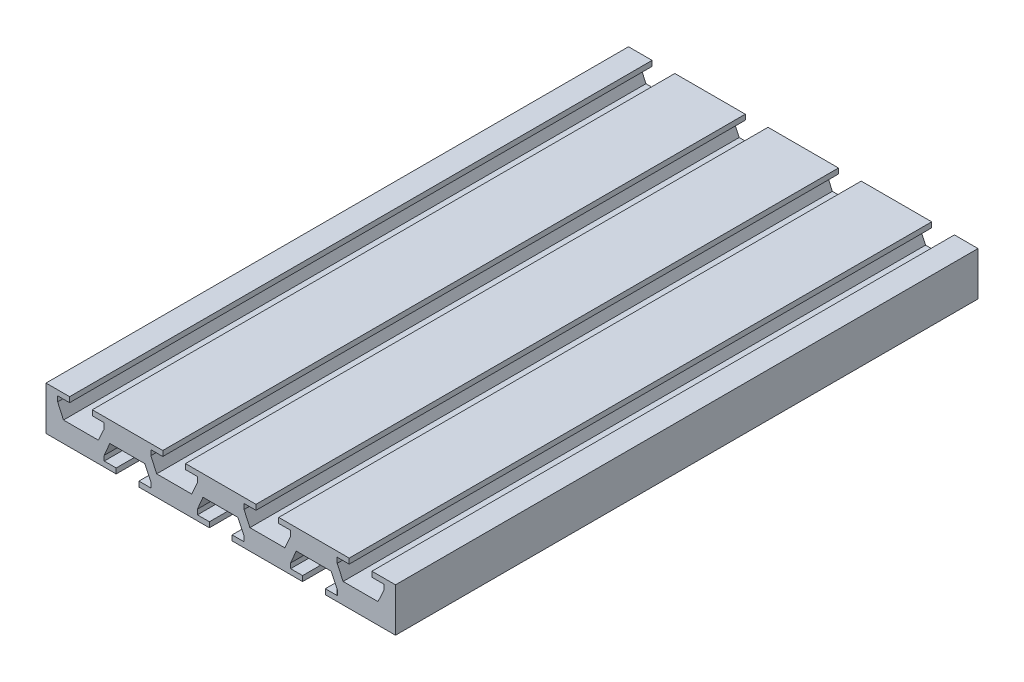
SolidWorks part; units mm, degrees
ref_plane "Front Plane" through (0, 0, 0) normal (0, 0, 1) x (1, 0, 0)
ref_plane "Top Plane" through (0, 0, 0) normal (0, 1, 0) x (1, 0, 0)
ref_plane "Right Plane" through (0, 0, 0) normal (1, 0, 0) x (0, 0, -1)
sketch "Sketch1" plane through (0, 0, 0) normal (0, 0, 1) x (1, 0, 0)
  line L0 (-48, 7.5) -> (-48, -0.5) construction
  line L1 (60, -7.5) -> (35.9, -7.5)
  line L2 (60, -7.5) -> (60, 7.5)
  line L3 (60, 7.5) -> (51.9, 7.5)
  line L4 (-60, -7.5) -> (-60, 7.5)
  line L5 (-24, -3.9) -> (-26.0998, 0.5)
  line L8 (-44.1, 7.5) -> (-44.1, 5.7)
  line L9 (-44.1, 5.7) -> (-40, 5.7)
  line L10 (-40, 5.7) -> (-40, 3.9)
  line L11 (-40, 3.9) -> (-42, -0.5)
  line L12 (-42, -0.5) -> (-54, -0.5)
  line L13 (-56, 3.9) -> (-54, -0.5)
  line L14 (-56, 5.7) -> (-56, 3.9)
  line L15 (-51.9, 5.7) -> (-56, 5.7)
  line L16 (-51.9, 7.5) -> (-51.9, 5.7)
  line L17 (-10, -0.5) -> (-22, -0.5)
  line L18 (-24, 3.9) -> (-22, -0.5)
  line L19 (-24, 5.7) -> (-24, 3.9)
  line L20 (-19.9, 5.7) -> (-24, 5.7)
  line L21 (-19.9, 7.5) -> (-19.9, 5.7)
  line L23 (-12.1, 7.5) -> (-12.1, 5.7)
  line L24 (-12.1, 5.7) -> (-8, 5.7)
  line L25 (-8, 5.7) -> (-8, 3.9)
  line L26 (-8, 3.9) -> (-10, -0.5)
  line L27 (22, -0.5) -> (10, -0.5)
  line L28 (8, 3.9) -> (10, -0.5)
  line L29 (8, 5.7) -> (8, 3.9)
  line L30 (12.1, 5.7) -> (8, 5.7)
  line L31 (12.1, 7.5) -> (12.1, 5.7)
  line L33 (19.9, 7.5) -> (19.9, 5.7)
  line L34 (19.9, 5.7) -> (24, 5.7)
  line L35 (24, 5.7) -> (24, 3.9)
  line L36 (24, 3.9) -> (22, -0.5)
  line L37 (54, -0.5) -> (42, -0.5)
  line L38 (40, 3.9) -> (42, -0.5)
  line L39 (40, 5.7) -> (40, 3.9)
  line L40 (44.1, 5.7) -> (40, 5.7)
  line L41 (44.1, 7.5) -> (44.1, 5.7)
  line L43 (51.9, 7.5) -> (51.9, 5.7)
  line L44 (51.9, 5.7) -> (56, 5.7)
  line L45 (56, 5.7) -> (56, 3.9)
  line L46 (56, 3.9) -> (54, -0.5)
  line L58 (-24, -5.7) -> (-24, -3.9)
  line L59 (-28.1, -5.7) -> (-24, -5.7)
  line L60 (-28.1, -7.5) -> (-28.1, -5.7)
  line L62 (-35.9, -7.5) -> (-35.9, -5.7)
  line L63 (-35.9, -5.7) -> (-40, -5.7)
  line L64 (-40, -5.7) -> (-40, -3.9898)
  line L65 (-40, -3.9898) -> (-38.0998, 0.5)
  line L66 (-26.0998, 0.5) -> (-38.0998, 0.5)
  line L67 (8, -3.9) -> (5.9002, 0.5)
  line L68 (5.9002, 0.5) -> (-6.0998, 0.5)
  line L69 (-8, -3.9898) -> (-6.0998, 0.5)
  line L70 (-8, -5.7) -> (-8, -3.9898)
  line L71 (-3.9, -5.7) -> (-8, -5.7)
  line L72 (-3.9, -7.5) -> (-3.9, -5.7)
  line L74 (3.9, -7.5) -> (3.9, -5.7)
  line L75 (3.9, -5.7) -> (8, -5.7)
  line L76 (8, -5.7) -> (8, -3.9)
  line L77 (40, -3.9) -> (37.9002, 0.5)
  line L78 (37.9002, 0.5) -> (25.9002, 0.5)
  line L79 (24, -3.9898) -> (25.9002, 0.5)
  line L80 (24, -5.7) -> (24, -3.9898)
  line L81 (28.1, -5.7) -> (24, -5.7)
  line L82 (28.1, -7.5) -> (28.1, -5.7)
  line L84 (35.9, -7.5) -> (35.9, -5.7)
  line L85 (35.9, -5.7) -> (40, -5.7)
  line L86 (40, -5.7) -> (40, -3.9)
  line L87 (-51.9, 7.5) -> (-60, 7.5)
  line L88 (-19.9, 7.5) -> (-44.1, 7.5)
  line L89 (12.1, 7.5) -> (-12.1, 7.5)
  line L90 (-35.9, -7.5) -> (-60, -7.5)
  line L91 (-3.9, -7.5) -> (-28.1, -7.5)
  line L92 (28.1, -7.5) -> (3.9, -7.5)
  line L93 (44.1, 7.5) -> (19.9, 7.5)
  point P0 (0, 0)
  point P21 (60, 0)
  dimension "D1" = 15
  dimension "D2" = 120
  dimension "D3" = 7.8
  dimension "D4" = 16
  dimension "D5" = 8
  dimension "D6" = 1.8
  dimension "D7" = 1.8
  dimension "D8" = 12
  dimension "D10" = 4
  dimension "D11" = 12
  dimension "D12" = 8
  dimension "D13" = 16
  dimension "D14" = 7.8
  dimension "D15" = 1.8
  dimension "D16" = 1.8
  dimension "D9" = 4
  dimension "D18" = 3
extrude "Boss-Extrude1" add sketch "Sketch1" along normal blind 200
sketch "Sketch2" plane through (0, 0, 0) normal (0, 0, -1) x (-1, 0, 0)
  line L0 (60, 0) -> (55.8, 0) construction
  line L1 (60, 7.5) -> (60, -7.5) construction
  line L2 (60, -2.8) -> (60, 2.8)
  line L3 (60, 2.8) -> (59.5572, 2.8)
  line L4 (59.5572, 2.8) -> (59.5572, 5)
  line L5 (59.5572, 5) -> (57.8001, 5)
  line L6 (57.8001, 5) -> (57, 2.8)
  line L7 (57, 2.8) -> (57, -2.8)
  line L8 (57.8001, -5) -> (57, -2.8)
  line L9 (59.5572, -5) -> (57.8001, -5)
  line L10 (59.5572, -2.8) -> (59.5572, -5)
  line L11 (60, -2.8) -> (59.5572, -2.8)
  point P2 (59.4503, 2.8)
  point P13 (57, 0)
  point P17 (58.6787, -5)
  point P18 (0, 0)
  point P19 (56, 2.8)
  point P20 (57.7362, 5)
  point P21 (59.685, 5)
  point P22 (57.8001, 5)
  point P23 (59.5572, 5)
  dimension "D1" = 5.6
  dimension "D2" = 10
  dimension "D3" = 3
